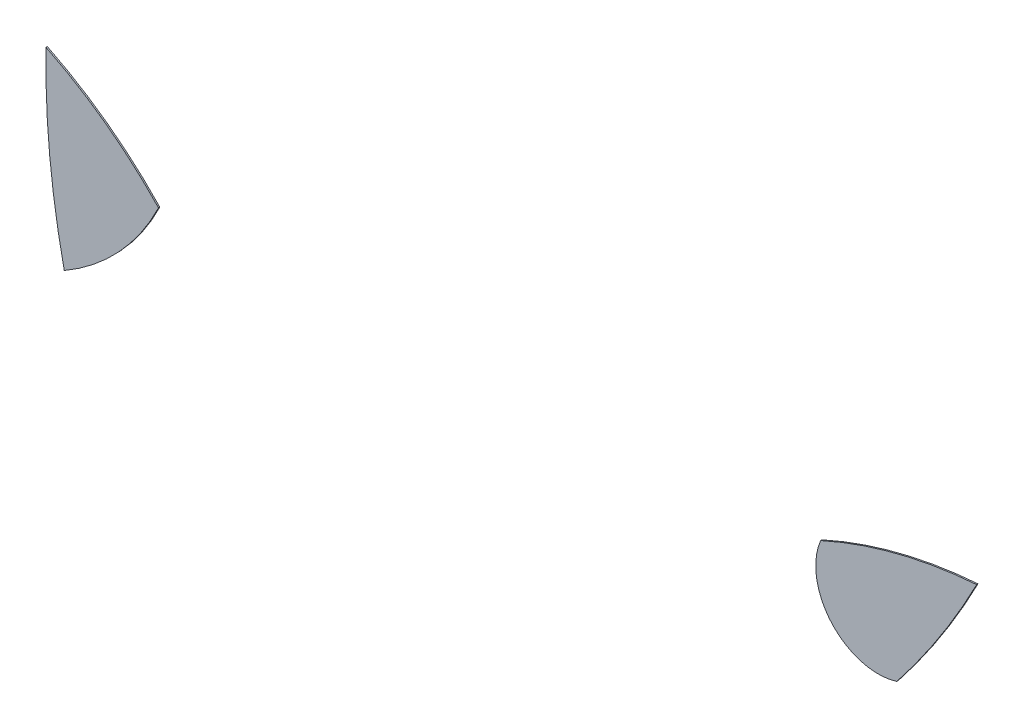
SolidWorks part; units mm, degrees
ref_plane "Alzado" through (0, 0, 0) normal (0, 0, 1) x (1, 0, 0)
ref_plane "Planta" through (0, 0, 0) normal (0, 1, 0) x (1, 0, 0)
ref_plane "Vista lateral" through (0, 0, 0) normal (1, 0, 0) x (0, 0, -1)
sketch "Model" plane through (0, 0, 0) normal (0, 0, 1) x (1, 0, 0)
  arc A0 (56.7853, 83.3471) -> (62.7915, 92.6605) centre (10.9717, 119.4854) ccw
  arc A1 (62.7915, 92.6605) -> (51.0558, 89.6616) centre (65.3464, 58.2003) ccw
  arc A2 (1.2525, 86.4309) -> (-7.2085, 92.6605) centre (-20.3576, 65.941) ccw
  arc A3 (-7.2085, 92.6605) -> (-5.8335, 78.8069) centre (52.3944, 91.5811) ccw
  arc A4 (51.0558, 89.6616) -> (56.7853, 83.3471) centre (55.3872, 87.8351) ccw
  arc A5 (-5.8335, 78.8069) -> (1.2525, 86.4309) centre (-14.7085, 94.1605) ccw
extrude "Saliente-Extruir1" add sketch "Model" along normal blind 0.1
